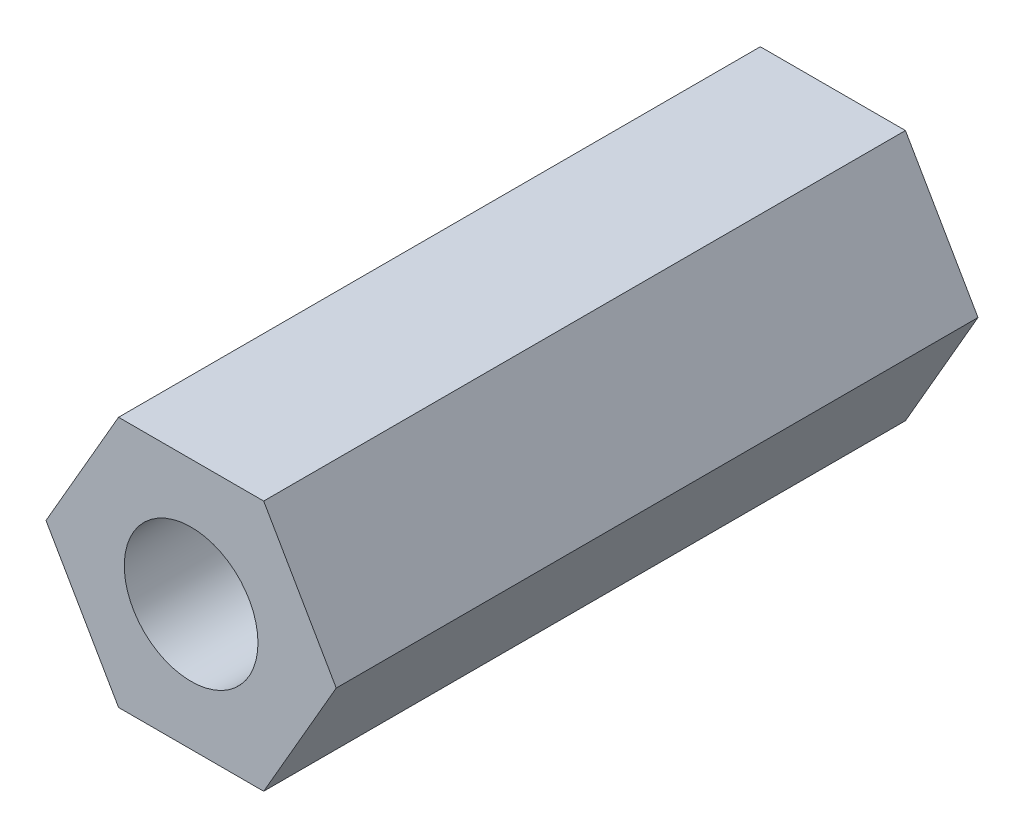
SolidWorks part; units mm, degrees
material "ABS"
ref_plane "Front Plane" through (0, 0, 0) normal (0, 0, 1) x (1, 0, 0)
ref_plane "Top Plane" through (0, 0, 0) normal (0, 1, 0) x (1, 0, 0)
ref_plane "Right Plane" through (0, 0, 0) normal (1, 0, 0) x (0, 0, -1)
sketch "Sketch1" plane through (0, 0, 0) normal (0, 0, 1) x (1, 0, 0)
  line L1 (2.7135, 0) -> (1.3568, 2.35)
  line L2 (1.3568, 2.35) -> (-1.3568, 2.35)
  line L3 (-1.3568, 2.35) -> (-2.7135, 0)
  line L4 (-2.7135, 0) -> (-1.3568, -2.35)
  line L5 (-1.3568, -2.35) -> (1.3568, -2.35)
  line L6 (1.3568, -2.35) -> (2.7135, 0)
  circle A0 centre (0, 0) radius 2.35 construction
  circle A1 centre (0, 0) radius 1.25
  dimension "D2" = 2.5
  dimension "D1" = 4.7
extrude "Boss-Extrude1" add sketch "Sketch1" along normal blind 12
